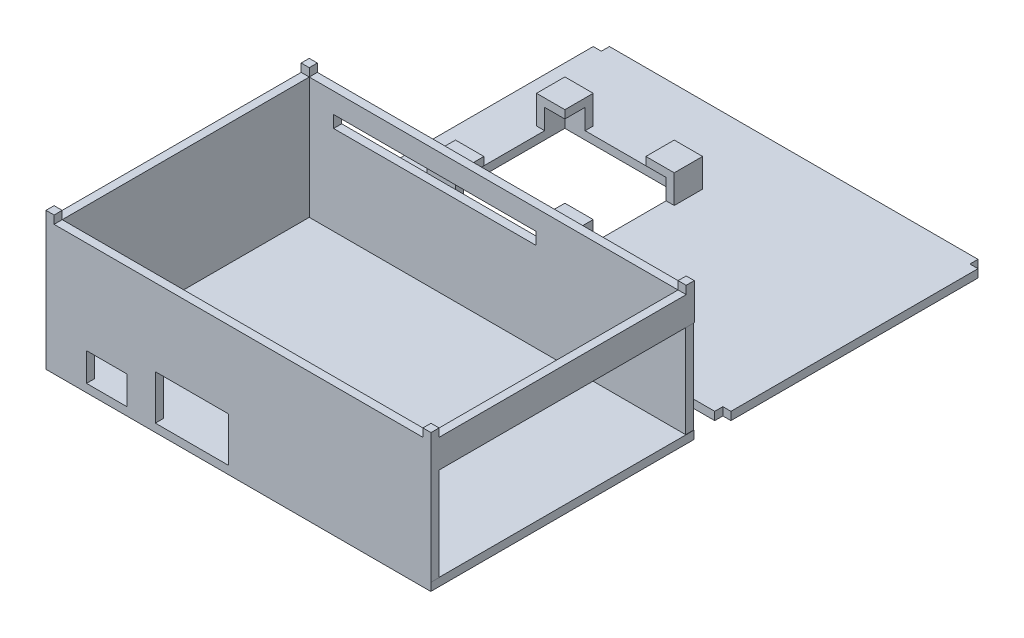
SolidWorks part; units mm, degrees
ref_plane "Plan de face" through (0, 0, 0) normal (0, 0, 1) x (1, 0, 0)
ref_plane "Plan de dessus" through (0, 0, 0) normal (0, 1, 0) x (1, 0, 0)
ref_plane "Plan de droite" through (0, 0, 0) normal (1, 0, 0) x (0, 0, -1)
sketch "Esquisse1" plane through (0, 0, 0) normal (0, 1, 0) x (1, 0, 0)
  line L1 (-79.0559, 55.7671) -> (15.9441, 55.7671)
  line L2 (-79.0559, 55.7671) -> (-79.0559, -9.2329)
  line L3 (-79.0559, -9.2329) -> (15.9441, -9.2329)
  line L4 (15.9441, 55.7671) -> (15.9441, -9.2329)
  dimension "D1" = 95
  dimension "D2" = 65
extrude "Boss.-Extru.1" add sketch "Esquisse1" along normal blind 2
sketch "Esquisse22" plane through (-79.0559, 0, 0) normal (-1, 0, 0) x (0, 0, 1)
  line L1 (-55.7671, 2) -> (9.2329, 2)
  line L2 (-55.7671, 2) -> (-55.7671, 32)
  line L3 (-55.7671, 32) -> (9.2329, 32)
  line L4 (9.2329, 2) -> (9.2329, 32)
  dimension "D1" = 65
  dimension "D2" = 30
extrude "Boss.-Extru.6" add sketch "Esquisse22" against normal blind 2
sketch "Esquisse23" plane through (0, 0, 9.2329) normal (0, 0, 1) x (1, 0, 0)
  line L0 (-77.0559, 32) -> (-77.0559, 2)
  line L1 (-77.0559, 32) -> (16.0022, 32)
  line L2 (-77.0559, 2) -> (16.0022, 2)
  line L3 (16.0022, 32) -> (16.0022, 2)
extrude "Boss.-Extru.7" add sketch "Esquisse23" against normal blind 2
ref_plane "Plan1" through (15.9441, 0, -55.7671) normal (-1, 0, 0) x (0, 0, 1)
sketch "Esquisse26" plane through (0, 0, -55.7671) normal (0, 0, -1) x (-1, 0, 0)
  line L0 (77.0559, 32) -> (77.0559, 2)
  line L1 (77.0559, 32) -> (-15.8674, 32)
  line L2 (77.0559, 2) -> (-15.8674, 2)
  line L3 (-15.8674, 32) -> (-15.8674, 2)
extrude "Boss.-Extru.8" add sketch "Esquisse26" against normal blind 2
sketch "Esquisse27" plane through (0, 0, 9.2329) normal (0, 0, 1) x (1, 0, 0)
  line L0 (-79.0559, 0) -> (-69.0559, 0) construction
  line L1 (-79.0559, 0) -> (15.9441, 0) construction
  line L2 (-69.0559, 0) -> (-69.0559, 2) construction
  line L4 (-69.0559, 2) -> (-59.0559, 2)
  line L5 (-69.0559, 2) -> (-69.0559, 9)
  line L6 (-69.0559, 9) -> (-59.0559, 9)
  line L7 (-59.0559, 2) -> (-59.0559, 9)
  dimension "D1" = 10
  dimension "D2" = 2
  dimension "D3" = 7
  dimension "D4" = 10
extrude "Enlèv. mat.-Extru.4" cut sketch "Esquisse27" against normal blind 2
sketch "Esquisse28" plane through (0, 0, 9.2329) normal (0, 0, 1) x (1, 0, 0)
  line L0 (-59.0559, 2) -> (-52.0559, 2) construction
  line L2 (-52.0559, 2) -> (-34.0559, 2)
  line L3 (-52.0559, 2) -> (-52.0559, 13)
  line L4 (-52.0559, 13) -> (-34.0559, 13)
  line L5 (-34.0559, 2) -> (-34.0559, 13)
  dimension "D1" = 7
  dimension "D2" = 11
  dimension "D3" = 18
extrude "Enlèv. mat.-Extru.5" cut sketch "Esquisse28" against normal blind 2
sketch "Esquisse30" plane through (16.0022, 0, 0) normal (1, 0, 0) x (0, 0, -1)
  line L1 (-9.2329, 32) -> (55.7671, 32)
  line L2 (-9.2329, 32) -> (-9.2329, 25)
  line L3 (-9.2329, 25) -> (55.7671, 25)
  line L4 (55.7671, 32) -> (55.7671, 25)
  dimension "D1" = 65
  dimension "D2" = 7
extrude "Boss.-Extru.9" add sketch "Esquisse30" against normal blind 2
sketch "Esquisse31" plane through (0, 0, 0) normal (0, 1, 0) x (1, 0, 0)
  line L1 (-78.5276, 62.3479) -> (16.4724, 62.3479)
  line L2 (-78.5276, 62.3479) -> (-78.5276, 127.3479)
  line L3 (-78.5276, 127.3479) -> (16.4724, 127.3479)
  line L4 (16.4724, 62.3479) -> (16.4724, 127.3479)
  dimension "D1" = 65
  dimension "D2" = 95
extrude "Boss.-Extru.11" add sketch "Esquisse31" along normal blind 2 separate body
sketch "Esquisse32" plane through (0, 32, 0) normal (0, 1, 0) x (1, 0, 0)
  line L1 (-77.0559, 53.7671) -> (-79.0559, 53.7671)
  line L2 (-77.0559, 53.7671) -> (-77.0559, 55.7671)
  line L3 (-77.0559, 55.7671) -> (-79.0559, 55.7671)
  line L4 (-79.0559, 53.7671) -> (-79.0559, 55.7671)
extrude "Boss.-Extru.12" add sketch "Esquisse32" along normal blind 2
pattern_linear "Répétition linéaire1" count 2 spacing 63 along (0, 0, 1) of "Boss.-Extru.12"
sketch "Esquisse33" plane through (0, 32, 0) normal (0, 1, 0) x (1, 0, 0)
  line L1 (14.0022, 53.7671) -> (16.0022, 53.7671)
  line L2 (14.0022, 53.7671) -> (14.0022, 55.7671)
  line L3 (14.0022, 55.7671) -> (16.0022, 55.7671)
  line L4 (16.0022, 53.7671) -> (16.0022, 55.7671)
extrude "Boss.-Extru.13" add sketch "Esquisse33" along normal blind 2
pattern_linear "Répétition linéaire4" count 2 spacing 63 along (0, 0, 1) of "Boss.-Extru.13"
sketch "Esquisse34" plane through (0, 2, 0) normal (0, 1, 0) x (1, 0, 0)
  line L1 (-78.5276, 127.3479) -> (-76.5276, 127.3479)
  line L2 (-78.5276, 127.3479) -> (-78.5276, 125.3479)
  line L3 (-78.5276, 125.3479) -> (-76.5276, 125.3479)
  line L4 (-76.5276, 127.3479) -> (-76.5276, 125.3479)
  dimension "D1" = 2
  dimension "D2" = 2
extrude "Enlèv. mat.-Extru.6" cut sketch "Esquisse34" against normal blind 2
pattern_linear "Répétition linéaire5" count 2 spacing 63 along (0, 0, 1) of "Enlèv. mat.-Extru.6"
sketch "Esquisse35" plane through (0, 2, 0) normal (0, 1, 0) x (1, 0, 0)
  line L1 (16.4724, 127.3479) -> (14.4724, 127.3479)
  line L2 (16.4724, 127.3479) -> (16.4724, 125.3479)
  line L3 (16.4724, 125.3479) -> (14.4724, 125.3479)
  line L4 (14.4724, 127.3479) -> (14.4724, 125.3479)
  dimension "D1" = 2
  dimension "D2" = 2
extrude "Enlèv. mat.-Extru.7" cut sketch "Esquisse35" against normal blind 2
pattern_linear "Répétition linéaire7" count 2 spacing 63 along (0, 0, 1) of "Enlèv. mat.-Extru.7"
sketch "Esquisse36" plane through (0, 2, 0) normal (0, 1, 0) x (1, 0, 0)
  line L1 (-76.5276, 64.3479) -> (-66.5276, 64.3479)
  line L2 (-76.5276, 64.3479) -> (-76.5276, 76.3479)
  line L3 (-76.5276, 76.3479) -> (-66.5276, 76.3479)
  line L4 (-66.5276, 64.3479) -> (-66.5276, 76.3479)
  line L5 (-66.5276, 76.3479) -> (-36.5276, 76.3479)
  line L6 (-66.5276, 76.3479) -> (-66.5276, 106.3479)
  line L7 (-66.5276, 106.3479) -> (-36.5276, 106.3479)
  line L8 (-36.5276, 76.3479) -> (-36.5276, 106.3479)
  dimension "D1" = 12
  dimension "D2" = 10
  dimension "D3" = 30
  dimension "D4" = 30
extrude "Enlèv. mat.-Extru.8" cut sketch "Esquisse36" against normal blind 2 contours L5 L8 L7 L6
sketch "Esquisse37" plane through (-66.5276, 0, 0) normal (1, 0, 0) x (0, 0, -1)
  line L1 (106.3479, 2) -> (101.3479, 2)
  line L2 (106.3479, 2) -> (106.3479, 9)
  line L3 (106.3479, 9) -> (101.3479, 9)
  line L4 (101.3479, 2) -> (101.3479, 9)
  dimension "D1" = 7
  dimension "D2" = 5
extrude "Boss.-Extru.14" add sketch "Esquisse37" against normal blind 2
sketch "Esquisse38" plane through (0, 0, -106.3479) normal (0, 0, -1) x (-1, 0, 0)
  line L0 (66.5276, 2) -> (36.5276, 2) construction
  line L1 (68.5276, 9) -> (61.5276, 9)
  line L2 (68.5276, 9) -> (68.5276, 2)
  line L3 (68.5276, 2) -> (61.5276, 2)
  line L4 (61.5276, 9) -> (61.5276, 2)
  dimension "D1" = 7
extrude "Boss.-Extru.15" add sketch "Esquisse38" along normal blind 2
sketch "Esquisse39" plane through (0, 9, 0) normal (0, 1, 0) x (1, 0, 0)
  line L0 (-61.5276, 106.3479) -> (-66.5276, 106.3479)
  line L1 (-61.5276, 106.3479) -> (-61.5276, 101.3479)
  line L2 (-66.5276, 106.3479) -> (-66.5276, 101.3479)
  line L3 (-61.5276, 101.3479) -> (-66.5276, 101.3479)
extrude "Boss.-Extru.16" add sketch "Esquisse39" against normal blind 2
sketch "Esquisse40" plane through (-66.5276, 0, 0) normal (1, 0, 0) x (0, 0, -1)
  line L1 (76.3479, 2) -> (81.3479, 2)
  line L2 (76.3479, 2) -> (76.3479, 9)
  line L3 (76.3479, 9) -> (81.3479, 9)
  line L4 (81.3479, 2) -> (81.3479, 9)
  dimension "D1" = 7
  dimension "D2" = 5
extrude "Boss.-Extru.17" add sketch "Esquisse40" against normal blind 2
sketch "Esquisse41" plane through (0, 0, -76.3479) normal (0, 0, 1) x (1, 0, 0)
  line L0 (-66.5276, 2) -> (-36.5276, 2) construction
  line L1 (-68.5276, 9) -> (-61.5276, 9)
  line L2 (-68.5276, 9) -> (-68.5276, 2)
  line L3 (-68.5276, 2) -> (-61.5276, 2)
  line L4 (-61.5276, 9) -> (-61.5276, 2)
  dimension "D1" = 7
extrude "Boss.-Extru.19" add sketch "Esquisse41" along normal blind 2
sketch "Esquisse43" plane through (0, 9, 0) normal (0, 1, 0) x (1, 0, 0)
  line L0 (-66.5276, 81.3479) -> (-66.5276, 76.3479)
  line L1 (-66.5276, 81.3479) -> (-61.5122, 81.3479)
  line L2 (-66.5276, 76.3479) -> (-61.5122, 76.3479)
  line L3 (-61.5122, 81.3479) -> (-61.5122, 76.3479)
extrude "Boss.-Extru.20" add sketch "Esquisse43" against normal blind 2
sketch "Esquisse44" plane through (-36.5276, 0, 0) normal (-1, 0, 0) x (0, 0, 1)
  line L1 (-106.3479, 2) -> (-101.3479, 2)
  line L2 (-106.3479, 2) -> (-106.3479, 9)
  line L3 (-106.3479, 9) -> (-101.3479, 9)
  line L4 (-101.3479, 2) -> (-101.3479, 9)
  dimension "D1" = 5
  dimension "D2" = 7
extrude "Boss.-Extru.21" add sketch "Esquisse44" against normal blind 2
sketch "Esquisse45" plane through (0, 0, -106.3479) normal (0, 0, -1) x (-1, 0, 0)
  line L1 (34.5276, 2) -> (41.5276, 2)
  line L2 (34.5276, 2) -> (34.5276, 9)
  line L3 (34.5276, 9) -> (41.5276, 9)
  line L4 (41.5276, 2) -> (41.5276, 9)
  dimension "D1" = 7
  dimension "D2" = 7
extrude "Boss.-Extru.22" add sketch "Esquisse45" along normal blind 2
sketch "Esquisse46" plane through (0, 9, 0) normal (0, 1, 0) x (1, 0, 0)
  line L0 (-36.5276, 101.3479) -> (-36.5276, 106.3479)
  line L1 (-36.5276, 101.3479) -> (-41.5295, 101.3479)
  line L2 (-36.5276, 106.3479) -> (-41.5295, 106.3479)
  line L3 (-41.5295, 101.3479) -> (-41.5295, 106.3479)
extrude "Boss.-Extru.23" add sketch "Esquisse46" against normal blind 2
sketch "Esquisse48" plane through (0, 0, -76.3479) normal (0, 0, -1) x (-1, 0, 0)
  line L1 (36.5276, 2) -> (41.5276, 2)
  line L2 (36.5276, 2) -> (36.5276, 9)
  line L3 (36.5276, 9) -> (41.5276, 9)
  line L4 (41.5276, 2) -> (41.5276, 9)
  dimension "D1" = 7
  dimension "D2" = 5
extrude "Boss.-Extru.24" add sketch "Esquisse48" against normal blind 2
sketch "Esquisse49" plane through (-36.5276, 0, 0) normal (1, 0, 0) x (0, 0, -1)
  line L1 (74.3479, 2) -> (81.3479, 2)
  line L2 (74.3479, 2) -> (74.3479, 9)
  line L3 (74.3479, 9) -> (81.3479, 9)
  line L4 (81.3479, 2) -> (81.3479, 9)
  dimension "D1" = 7
  dimension "D2" = 7
extrude "Boss.-Extru.25" add sketch "Esquisse49" along normal blind 2
sketch "Esquisse50" plane through (0, 9, 0) normal (0, 1, 0) x (1, 0, 0)
  line L0 (-41.5276, 76.3479) -> (-36.5276, 76.3479)
  line L1 (-41.5276, 76.3479) -> (-41.5276, 81.3479)
  line L2 (-36.5276, 76.3479) -> (-36.5276, 81.3479)
  line L3 (-41.5276, 81.3479) -> (-36.5276, 81.3479)
extrude "Boss.-Extru.26" add sketch "Esquisse50" against normal blind 2
sketch "Esquisse51" plane through (0, 0, -55.7671) normal (0, 0, -1) x (-1, 0, 0)
  line L1 (79.0559, 0) -> (71.0559, 0)
  line L2 (79.0559, 0) -> (79.0559, 24)
  line L3 (79.0559, 24) -> (71.0559, 24)
  line L4 (71.0559, 0) -> (71.0559, 24)
  line L5 (71.0559, 24) -> (21.0559, 24)
  line L6 (71.0559, 24) -> (71.0559, 27)
  line L7 (71.0559, 27) -> (21.0559, 27)
  line L8 (21.0559, 24) -> (21.0559, 27)
  dimension "D1" = 24
  dimension "D2" = 8
  dimension "D3" = 3
  dimension "D4" = 50
extrude "Enlèv. mat.-Extru.9" cut sketch "Esquisse51" against normal blind 2 contours L8 L5 L6 L7
